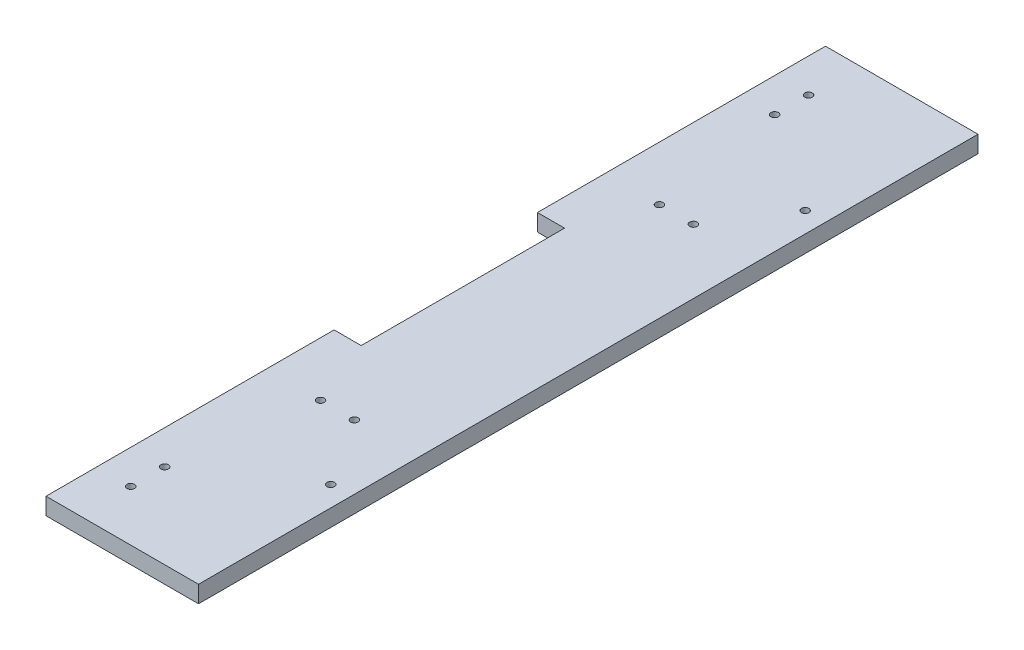
SolidWorks part; units mm, degrees
material "Polywood"
ref_plane "Front Plane" through (0, 0, 0) normal (0, 0, 1) x (1, 0, 0)
ref_plane "Top Plane" through (0, 0, 0) normal (0, 1, 0) x (1, 0, 0)
ref_plane "Right Plane" through (0, 0, 0) normal (1, 0, 0) x (0, 0, -1)
sketch "Sketch1" plane through (0, 0, 0) normal (1, 0, 0) x (0, 0, -1)
  line L0 (0, 0) -> (0, 50000) construction
  line L1 (-110, 0) -> (-115, 0)
  line L2 (-110, 0) -> (-110, 110)
  line L3 (-110, 110) -> (-115, 110)
  line L4 (-115, 0) -> (-115, 110)
  line L5 (115, 0) -> (115, 110)
  line L6 (110, 110) -> (115, 110)
  line L7 (110, 0) -> (110, 110)
  line L8 (110, 0) -> (115, 0)
  dimension "D1" = 110
  dimension "D2" = 5
  dimension "D3" = 110
extrude "Boss-Extrude1" add sketch "Sketch1" along normal blind 120 and the other way blind 110
sketch "Sketch2" plane through (-110, 0, 0) normal (-1, 0, 0) x (0, 0, 1)
  line L0 (-110, 110) -> (-110, 0) construction
  line L1 (-115, 0) -> (-110, 0)
  line L2 (-115, 0) -> (-115, 37)
  line L3 (-115, 37) -> (-110, 37)
  line L4 (-110, 0) -> (-110, 37)
  line L5 (0, 0) -> (0, 50000) construction
  line L6 (110, 0) -> (110, 37)
  line L7 (115, 37) -> (110, 37)
  line L8 (115, 0) -> (115, 37)
  line L9 (115, 0) -> (110, 0)
  dimension "D1" = 37
extrude "Boss-Extrude2" add sketch "Sketch2" along normal blind 50
sketch "Sketch3" plane through (-160, 0, 0) normal (-1, 0, 0) x (0, 0, 1)
  line L5 (110, 37) -> (110, 0) construction
  line L6 (-110, 37) -> (110, 37)
  line L7 (-110, 37) -> (-110, 32)
  line L8 (-110, 32) -> (110, 32)
  line L9 (110, 37) -> (110, 32)
  dimension "D1" = 5
extrude "Boss-Extrude3" add sketch "Sketch3" against normal blind 50
sketch "Sketch4" plane through (-110, 0, 0) normal (-1, 0, 0) x (0, 0, 1)
  line L1 (-115, 110) -> (115, 110)
  line L2 (-115, 110) -> (-115, 37)
  line L3 (-115, 37) -> (115, 37)
  line L4 (115, 110) -> (115, 37)
extrude "Boss-Extrude6" add sketch "Sketch4" along normal blind 5
fillet "Fillet3" [suppressed] radius 15
ref_plane "Plane1" through (115, 115, 0) normal (-0.7071, -0.7071, 0) x (0, 0, 1)
sketch "Sketch9" plane through (0, 0, 115) normal (0, 0, 1) x (1, 0, 0)
  line L0 (120, 110) -> (116.4645, 106.4645)
  line L1 (116.4645, 106.4645) -> (120, 102.9289)
  line L2 (120, 110) -> (120, 0) construction
  line L3 (120, 102.9289) -> (120, 110)
  dimension "D1" = 5
  dimension "D2" = 45
extrude "Cut-Extrude3" cut sketch "Sketch9" against normal through all
sketch "Sketch5" plane through (115, 115, 0) normal (-0.7071, -0.7071, 0) x (0, 0, 1)
  line L0 (-115, -7.0711) -> (-110, -7.0711) construction
  line L1 (174, -7.0711) -> (-174, -7.0711)
  line L2 (174, -7.0711) -> (174, -234.0711)
  line L3 (174, -234.0711) -> (-174, -234.0711)
  line L4 (-174, -7.0711) -> (-174, -234.0711)
  line L6 (164, -17.0711) -> (-164, -17.0711)
  line L7 (164, -17.0711) -> (164, -224.0711)
  line L8 (164, -224.0711) -> (-164, -224.0711)
  line L9 (-164, -17.0711) -> (-164, -224.0711)
  point P8 (0, -7.0711)
  dimension "D1" = 227
  dimension "D2" = 348
  dimension "D3" = 10
  dimension "D4" = 10
  dimension "D5" = 207
  dimension "D6" = 328
extrude "Boss-Extrude7" add sketch "Sketch5" along normal blind 5 separate body
sketch "Sketch10" plane through (0, 0, 115) normal (0, 0, 1) x (1, 0, 0)
  line L0 (120, 110) -> (111.4645, 110)
  line L1 (-115, 110) -> (120, 110) construction
  line L2 (111.4645, 110) -> (111.4645, 0)
  line L3 (-160, 0) -> (120, 0) construction
  line L4 (111.4645, 0) -> (120, 0)
  line L5 (120, 0) -> (120, 102.9289)
  line L6 (276.9777, -54.0488) -> (116.4645, 106.4645) construction
  line L7 (120, 102.9289) -> (120, 0) construction
  line L8 (120, 102.9289) -> (116.4645, 106.4645)
  line L9 (116.4645, 106.4645) -> (120, 110)
  dimension "D1" = 5
extrude "Boss-Extrude8" add sketch "Sketch10" along normal blind 59
mirror "Mirror3" about plane through (0, 0, 0) normal (0, 0, 1) of "Boss-Extrude8"
fillet "Fillet5" radius 15 2 edges at (111.4645, 55, -115) (111.4645, 55, 115)
sketch "Sketch12" plane through (0, 0, 174) normal (0, 0, 1) x (1, 0, 0)
  line L0 (120, 0) -> (222.9289, 0)
  line L1 (276.9777, -54.0488) -> (116.4645, 106.4645) construction
  line L2 (222.9289, 0) -> (120, 102.9289)
  line L3 (120, 102.9289) -> (120, 0)
extrude "Boss-Extrude9" add sketch "Sketch12" against normal blind 5 separate body
sketch "Sketch13" plane through (0, 0, -174) normal (0, 0, -1) x (-1, 0, 0)
  line L0 (-120, 102.9289) -> (-120, 0)
  line L1 (-120, 0) -> (-222.9289, 0)
  line L2 (-116.4645, 106.4645) -> (-276.9777, -54.0488) construction
  line L3 (-120, 0) -> (-222.9289, 0) construction
  line L4 (-222.9289, 0) -> (-120, 102.9289)
extrude "Boss-Extrude10" add sketch "Sketch13" against normal blind 5 separate body
fillet "Fillet6" radius 3 2 edges at (111.4645, 55, 174) (111.4645, 55, -174)
sketch "Sketch14" plane through (0, 110, 0) normal (0, 1, 0) x (1, 0, 0)
  line L11 (-115, 115) -> (-115, -115)
  line L13 (-167.31, 115) -> (-115, 115)
  line L14 (-167.31, 115) -> (-167.31, 193.7612)
  line L15 (-167.31, 193.7612) -> (289.6843, 193.7612)
  line L16 (289.6843, 105) -> (289.6843, 193.7612)
  line L17 (-167.31, -115) -> (-115, -115)
  line L18 (-167.31, -115) -> (-167.31, -200.6021)
  line L19 (-167.31, -200.6021) -> (289.6843, -200.6021)
  line L20 (289.6843, -115) -> (289.6843, -200.6021)
  line L21 (-115, -115) -> (-115, 115) construction
  line L22 (289.6843, 105) -> (289.6843, -115)
  line L23 (-160, 115) -> (-115, 115) construction
  line L24 (-160, -115) -> (-115, -115) construction
extrude "Cut-Extrude4" cut sketch "Sketch14" against normal through all
sketch "Sketch15" plane through (0, 0, 115) normal (0, 0, 1) x (1, 0, 0)
  line L0 (-115, 0) -> (-115, 37) construction
  line L1 (-160, 0) -> (-115, 0)
  line L2 (-160, 0) -> (-160, 32)
  line L3 (-160, 32) -> (-115, 32)
  line L4 (-115, 0) -> (-115, 32)
  line L5 (-160, 37) -> (-115, 37) construction
  dimension "D1" = 5
extrude "Cut-Extrude5" cut sketch "Sketch15" against normal through all and the other way through all
sketch "Sketch16" plane through (0, 37, 0) normal (0, 1, 0) x (1, 0, 0)
  line L0 (-160, -115) -> (-115, -115) construction
  line L3 (-155.1402, -95) -> (49844.8598, -95) construction
  line L4 (0, 0) -> (-50000, 0) construction
  line L5 (-160, -115) -> (-160, 115) construction
  circle A0 centre (-150, -100) radius 1.1
  circle A2 centre (-150, -90) radius 1.1
  circle A3 centre (-150, 90) radius 1.1
  circle A4 centre (-150, 100) radius 1.1
  dimension "D2" = 2.2
  dimension "D1" = 15
  dimension "D3" = 10
  dimension "D4" = 5
extrude "Holes for part 1" cut sketch "Sketch16" against normal through all
sketch "Sketch17" plane through (0, 37, 0) normal (0, 1, 0) x (1, 0, 0)
  line L0 (-115, 0) -> (49885, 0) construction
  line L1 (-115, 115) -> (-115, -115) construction
  circle A0 centre (-121, 70) radius 1.1
  circle A1 centre (-121, -70) radius 1.1
  point P6 (-115, 0)
  dimension "D1" = 2.2
  dimension "D2" = 70
  dimension "D3" = 6
extrude "Holes for forward part 4" cut sketch "Sketch17" against normal through all
sketch "Sketch18" plane through (0, 37, 0) normal (0, 1, 0) x (1, 0, 0)
  line L0 (-110, 63.2582) -> (-110, -49936.7418) construction
  line L1 (-115, 115) -> (-115, -115) construction
  line L2 (-115, 0) -> (49885, 0) construction
  line L3 (-139, 57.7771) -> (-139, -49942.2229) construction
  circle A0 centre (-134, 50) radius 1.1
  circle A1 centre (-144, 50) radius 1.1
  circle A2 centre (-144, -50) radius 1.1
  circle A3 centre (-134, -50) radius 1.1
  point P8 (-115, 0)
  dimension "D3" = 2.2
  dimension "D1" = 5
  dimension "D2" = 24
  dimension "D4" = 5
  dimension "D5" = 50
extrude "Holes for forward part 2" cut sketch "Sketch18" against normal through all
sketch "Sketch19" plane through (0, 37, 0) normal (0, 1, 0) x (1, 0, 0)
  line L0 (-160, -115) -> (-160, 115) construction
  line L1 (-168, -30) -> (-152, -30)
  line L2 (-168, -30) -> (-168, 30)
  line L3 (-168, 30) -> (-152, 30)
  line L4 (-152, -30) -> (-152, 30)
  line L5 (-168, -30) -> (-152, 30) construction
  line L6 (-168, 30) -> (-152, -30) construction
  point P0 (-160, 0)
  dimension "D1" = 60
  dimension "D2" = 16
extrude "Cut-Extrude6" cut sketch "Sketch19" against normal through all
